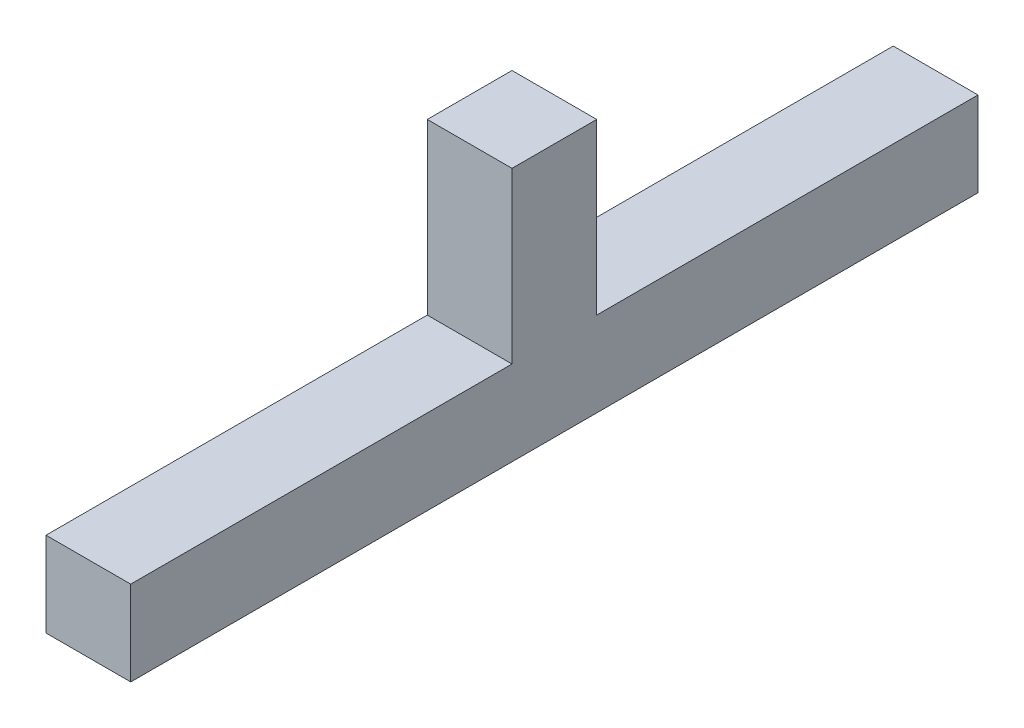
SolidWorks part; units mm, degrees
ref_plane "Front Plane" through (0, 0, 0) normal (0, 0, 1) x (1, 0, 0)
ref_plane "Top Plane" through (0, 0, 0) normal (0, 1, 0) x (1, 0, 0)
ref_plane "Right Plane" through (0, 0, 0) normal (1, 0, 0) x (0, 0, -1)
sketch "Sketch1" plane through (0, 0, 0) normal (1, 0, 0) x (0, 0, -1)
  line L0 (-50, 5) -> (-27.5, 5)
  line L1 (0, 0) -> (-50, 0)
  line L2 (0, 0) -> (0, 5)
  line L3 (-22.5, 15) -> (-27.5, 15)
  line L4 (-50, 0) -> (-50, 5)
  line L5 (-27.5, 5) -> (-27.5, 15)
  line L7 (-22.5, 15) -> (-22.5, 5)
  line L8 (-22.5, 5) -> (0, 5)
  dimension "D1" = 22.5
  dimension "D2" = 22.5
  dimension "D3" = 5
  dimension "D4" = 5
  dimension "D5" = 10
  dimension "D6" = 10
extrude "Boss-Extrude4" add sketch "Sketch1" along normal blind 5
